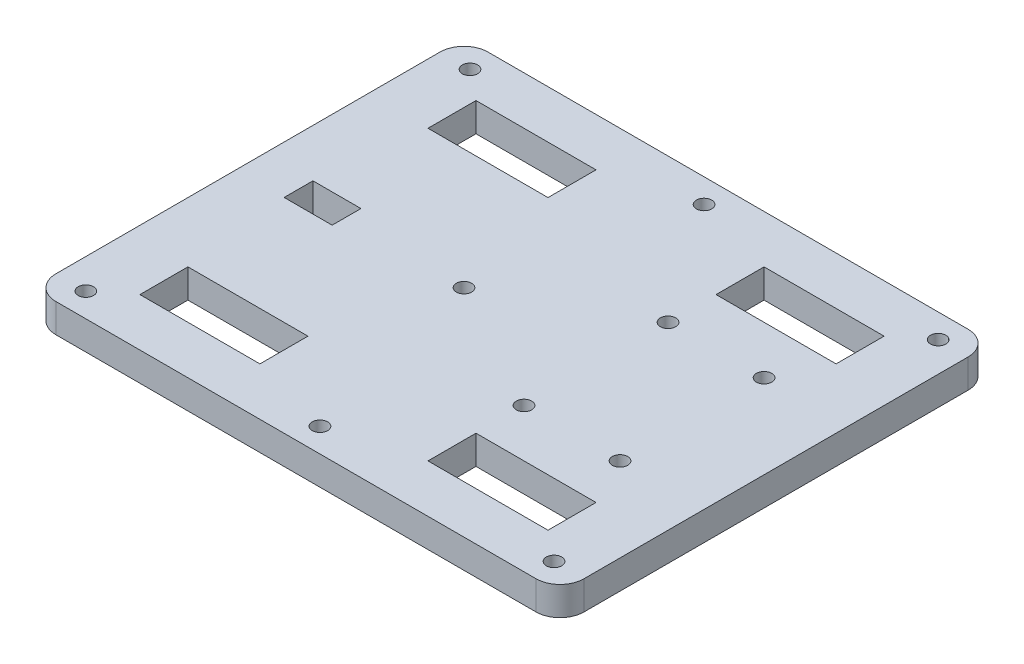
SolidWorks part; units mm, degrees
material "Maple"
ref_plane "Front Plane" through (0, 0, 0) normal (0, 0, 1) x (1, 0, 0)
ref_plane "Top Plane" through (0, 0, 0) normal (0, 1, 0) x (1, 0, 0)
ref_plane "Right Plane" through (0, 0, 0) normal (1, 0, 0) x (0, 0, -1)
sketch "Sketch1" plane through (0, 0, 0) normal (0, 1, 0) x (1, 0, 0)
  line L0 (-55, 0) -> (55, 0) construction
  line L1 (-55, 45) -> (55, 45)
  line L2 (-55, 45) -> (-55, -45)
  line L3 (-55, -45) -> (55, -45)
  line L4 (55, 45) -> (55, -45)
  point P0 (0, 0)
  dimension "D1" = 90
  dimension "D2" = 110
extrude "Boss-Extrude1" add sketch "Sketch1" along normal blind 6
sketch "Sketch2" plane through (0, 6, 0) normal (0, 1, 0) x (1, 0, 0)
  line L0 (-55, 0) -> (55, 0) construction
  line L1 (-55, 45) -> (-55, -45) construction
  line L2 (55, -45) -> (55, 45) construction
  line L3 (0, 0) -> (0, 45) construction
  line L4 (17.5, 35) -> (42.5, 35)
  line L5 (17.5, 35) -> (17.5, 25)
  line L6 (17.5, 25) -> (42.5, 25)
  line L7 (42.5, 35) -> (42.5, 25)
  line L8 (17.5, 35) -> (42.5, 25) construction
  line L9 (17.5, 25) -> (42.5, 35) construction
  line L10 (55, 45) -> (-55, 45) construction
  point P6 (30, 30)
  dimension "D1" = 10
  dimension "D2" = 60
  dimension "D3" = 60
  dimension "D4" = 25
extrude "Cut-Extrude1" cut sketch "Sketch2" against normal through all
mirror "Mirror1" about plane through (0, 0, 0) normal (0, 0, 1) of "Cut-Extrude1"
mirror "Mirror2" about plane through (0, 0, 0) normal (1, 0, 0) of "Mirror1", "Cut-Extrude1"
hole_wizard "M3 Clearance Hole1" positions "Sketch4" profile "Sketch3" hole size "M3" standard "ANSI Metric" end condition through all
sketch "Sketch4" plane through (0, 6, 0) normal (0, 1, 0) x (1, 0, 0)
  line L0 (13.7067, -15) -> (41.2933, -15) construction
  line L1 (13.7067, 15) -> (41.2933, 15) construction
  line L3 (17.5, 15) -> (17.5, -15) construction
  line L5 (37.5, 15) -> (37.5, -15) construction
  line L7 (27.5, 15) -> (27.5, -15) construction
  point P0 (17.5, 15)
  point P2 (37.5, 15)
  point P4 (17.5, -15)
  point P6 (37.5, -15)
  dimension "D2" = 20
sketch "Sketch3" plane through (17.5, 6, -15) normal (1, 0, 0) x (0, 0, 1)
  line L0 (0, 0) -> (0, 6)
  line L1 (0, 6) -> (1.6, 6)
  line L2 (1.6, 6) -> (1.6, 0)
  line L5 (1.6, 0) -> (0, 0)
  line L11 (0, -6.35) -> (0, 107.95) construction
  dimension "Thru Hole Dia." = 3.2
  dimension "Thru Hole Depth" = 6
hole_wizard "M3 Clearance Hole2" positions "Sketch6" profile "Sketch5" hole size "M3" standard "ANSI Metric" end condition through all
sketch "Sketch6" plane through (0, 6, 0) normal (0, 1, 0) x (1, 0, 0)
  line L0 (-48.75, -40) -> (-48.75, 40) construction
  line L1 (-48.75, 40) -> (48.75, 40) construction
  line L2 (48.75, 40) -> (48.75, -40) construction
  line L3 (48.75, -40) -> (-48.75, -40) construction
  line L5 (-48.75, 40) -> (48.75, -40) construction
  line L7 (-48.75, -40) -> (48.75, 40) construction
  line L9 (-30, 35) -> (-30, 40) construction
  line L10 (-42.5, 35) -> (-17.5, 35) construction
  line L11 (-30, 40) -> (-30, 45) construction
  line L12 (55, 45) -> (-55, 45) construction
  line L14 (-42.5, 30) -> (-48.75, 30) construction
  line L15 (-42.5, 25) -> (-42.5, 35) construction
  line L16 (-48.75, 30) -> (-55, 30) construction
  line L17 (-55, 45) -> (-55, -45) construction
  line L18 (-10, 0) -> (0, 0) construction
  point P0 (48.75, 40)
  point P2 (0, 40)
  point P4 (-48.75, 40)
  point P6 (-48.75, -40)
  point P8 (0, -40)
  point P10 (48.75, -40)
  point P58 (-10, 0)
  dimension "D1" = 10
sketch "Sketch5" plane through (48.75, 6, -40) normal (1, 0, 0) x (0, 0, 1)
  line L0 (0, 0) -> (0, 6)
  line L1 (0, 6) -> (1.6, 6)
  line L2 (1.6, 6) -> (1.6, 0)
  line L5 (1.6, 0) -> (0, 0)
  line L11 (0, -6.35) -> (0, 107.95) construction
  dimension "Thru Hole Dia." = 3.2
  dimension "Thru Hole Depth" = 6
fillet "Fillet1" radius 5 4 edges at (55, 3, 45) (-55, 3, 45) (55, 3, -45) (-55, 3, -45)
sketch "Sketch7" plane through (0, 0, 0) normal (0, -1, 0) x (1, 0, 0)
  line L0 (-50, -0.54) -> (-30, -0.54) construction
  line L1 (-50, -3.54) -> (-50, 2.46) construction
  line L2 (-30, -3.54) -> (-30, 2.46) construction
  point P6 (-40, -0.54)
sketch "Sketch62" plane through (-39.2322, 3, -44.54) normal (0, -1, 0) x (-1, 0, 0)
  line L1 (-4.2322, -41) -> (5.7678, -41)
  line L2 (-4.2322, -41) -> (-4.2322, -47)
  line L3 (-4.2322, -47) -> (5.7678, -47)
  line L4 (5.7678, -41) -> (5.7678, -47)
  line L5 (-4.2322, -41) -> (5.7678, -47) construction
  line L6 (-4.2322, -47) -> (5.7678, -41) construction
  point P0 (0.7678, -44)
  dimension "D1" = 10
  dimension "D2" = 6
extrude "Cut-Extrude12" cut sketch "Sketch62" against normal through all and the other way through all
other "Smart-Feature2<virtual_pin-55>"
